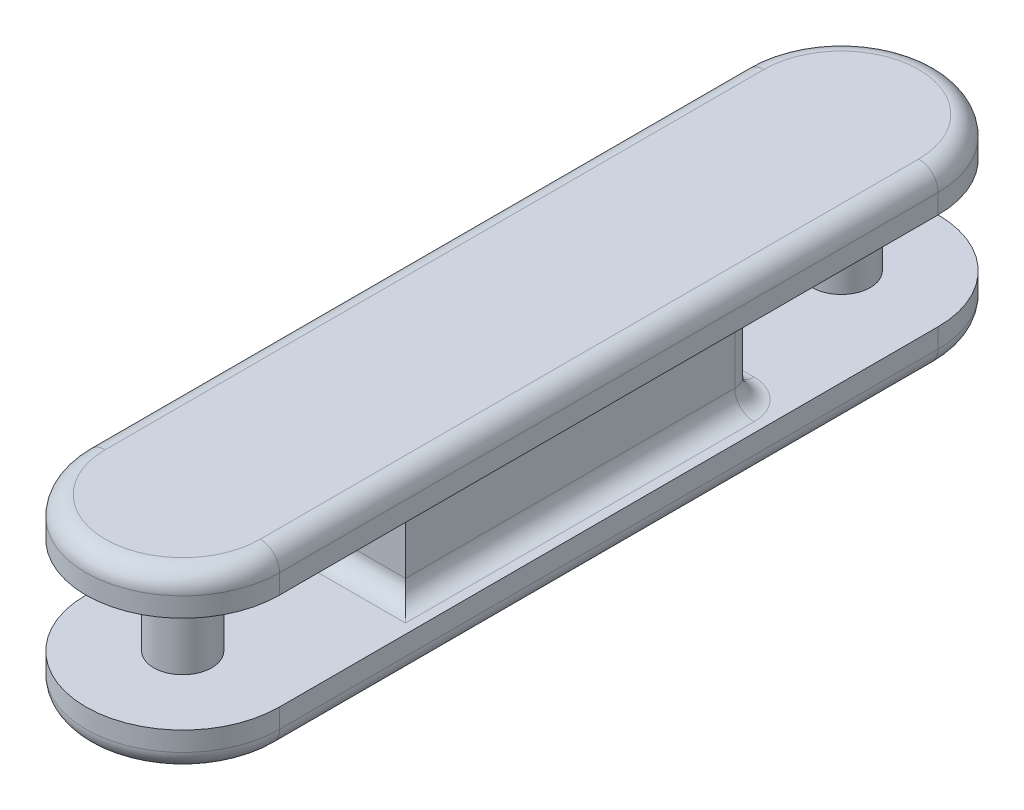
SolidWorks part; units mm, degrees
ref_plane "前基準面" through (0, 0, 0) normal (0, 0, 1) x (1, 0, 0)
ref_plane "上基準面" through (0, 0, 0) normal (0, 1, 0) x (1, 0, 0)
ref_plane "右基準面" through (0, 0, 0) normal (1, 0, 0) x (0, 0, -1)
ref_plane "平面1" through (0, 25, 0) normal (0, 1, 0) x (1, 0, 0)
sketch "草圖1" plane through (0, 25, 0) normal (0, 1, 0) x (1, 0, 0)
  line L2 (-50, 170) -> (-50, -170)
  line L4 (50, 170) -> (50, -170)
  line L5 (-50, 170) -> (50, -170) construction
  line L6 (-50, -170) -> (50, 170) construction
  arc A0 (50, 170) -> (-50, 170) centre (0, 170) ccw
  arc A1 (-50, -170) -> (50, -170) centre (0, -170) ccw
  point P0 (0, 0)
  dimension "D1" = 340
  dimension "D2" = 100
extrude "填料-伸長1" add sketch "草圖1" along normal blind 20
ref_plane "平面2" through (0, -25, 0) normal (0, 1, 0) x (1, 0, 0)
sketch "草圖2" plane through (0, -25, 0) normal (0, 1, 0) x (1, 0, 0)
  line L0 (50, -170) -> (50, 170) construction
  line L1 (-50, 170) -> (-50, -170) construction
  line L2 (50, -170) -> (50, 170)
  line L3 (-50, 170) -> (-50, -170)
  arc A0 (50, 170) -> (-50, 170) centre (0, 170) ccw construction
  arc A1 (-50, -170) -> (50, -170) centre (0, -170) ccw construction
  arc A2 (50, 170) -> (-50, 170) centre (0, 170) ccw
  arc A3 (-50, -170) -> (50, -170) centre (0, -170) ccw
extrude "填料-伸長2" add sketch "草圖2" against normal blind 20 separate body
sketch "草圖3" plane through (0, 45, 0) normal (0, 1, 0) x (1, 0, 0)
  line L1 (-35, -90) -> (35, -90)
  line L2 (-35, -90) -> (-35, 90)
  line L3 (-35, 90) -> (35, 90)
  line L4 (35, -90) -> (35, 90)
  line L5 (-35, -90) -> (35, 90) construction
  line L6 (-35, 90) -> (35, -90) construction
  circle A0 centre (0, 170) radius 15
  circle A1 centre (0, -170) radius 15
  point P6 (0, 0)
  dimension "D1" = 30
  dimension "D2" = 30
  dimension "D3" = 70
  dimension "D4" = 180
extrude "填料-伸長3" add sketch "草圖3" against normal up to surface (90 mm away) up to face at (0, -45, 0)
fillet "圓角1" radius 10 8 edges at (-50, -45, 0) (0, -45, 220) (50, -45, 0) (0, -45, -220) (-50, 45, 0) (0, 45, -220) (50, 45, 0) (0, 45, 220)
fillet "圓角2" radius 10 11 edges at (0, -25, 90) (0, 25, 90) (35, -25, 0) (35, 25, 0) (-35, 0, 90) (-35, -25, 0) (-35, 25, 0) (-35, 0, -90) (0, -25, -90) (35, 0, -90) (0, 25, -90)
